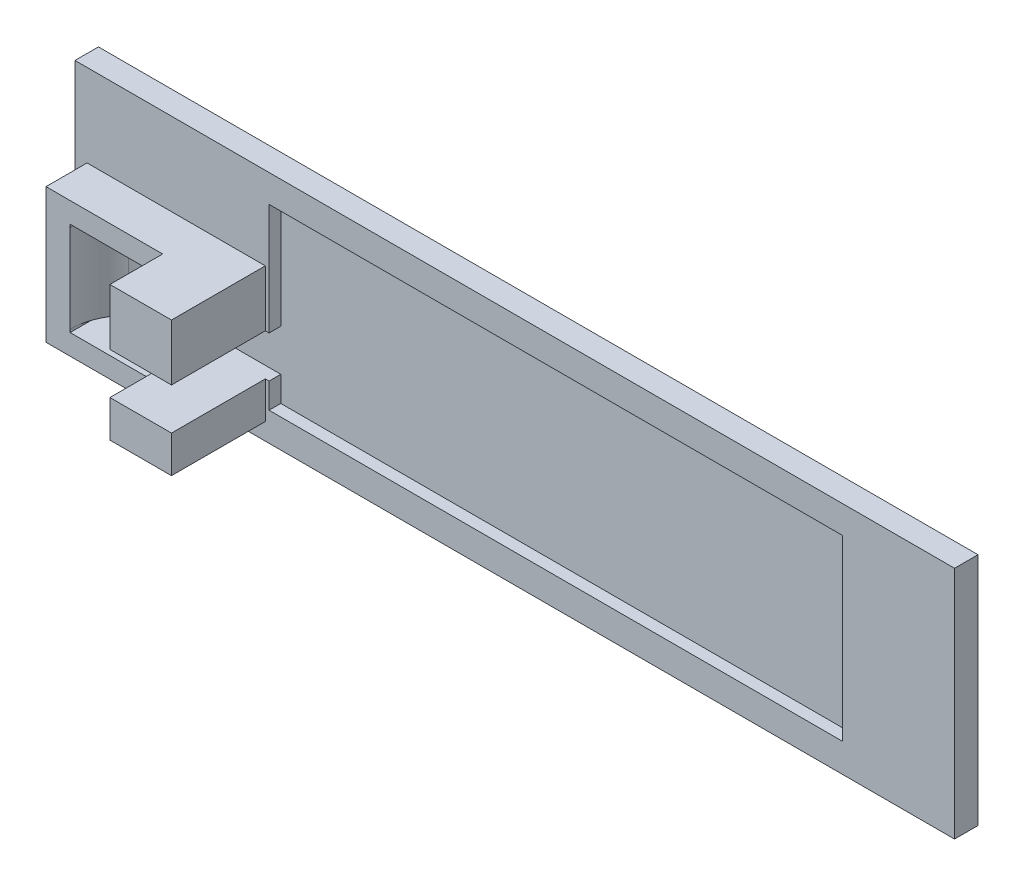
SolidWorks part; units mm, degrees
ref_plane "Front Plane" through (0, 0, 0) normal (0, 0, 1) x (1, 0, 0)
ref_plane "Top Plane" through (0, 0, 0) normal (0, 1, 0) x (1, 0, 0)
ref_plane "Right Plane" through (0, 0, 0) normal (1, 0, 0) x (0, 0, -1)
sketch "Sketch1" plane through (0, 0, 0) normal (0, 0, 1) x (1, 0, 0)
  line L13 (0, -3.5114) -> (107.0846, -3.5114) construction
  line L14 (-21.4577, 30.8029) -> (128.5423, 30.8029)
  line L15 (-21.4577, 30.8029) -> (-21.4577, -9.1971)
  line L16 (-21.4577, -9.1971) -> (128.5423, -9.1971)
  line L17 (128.5423, 30.8029) -> (128.5423, -9.1971)
  line L18 (107.0846, 25.1173) -> (107.0846, -3.5114) construction
  line L19 (0, 25.1173) -> (0, -3.5114) construction
  line L20 (0, 10.8029) -> (107.0846, 10.8029) construction
  line L21 (107.4114, 19.3947) -> (107.4114, 16.5631) construction
  line L22 (107.0846, 25.1173) -> (0, 25.1173) construction
  line L23 (-21.4577, -9.1971) -> (128.5423, 30.8029) construction
  line L24 (-21.4577, 30.8029) -> (128.5423, -9.1971) construction
  line L140 (53.5423, 25.1173) -> (53.5423, -3.5114) construction
  line L141 (107.4114, 19.3947) -> (107.4114, 16.5631)
  line L165 (11.6394, 7.1) -> (0, 7.1)
  line L167 (0, 7.1) -> (0, 0)
  line L168 (12.1959, 0) -> (0, 0)
  line L175 (47.7841, -3.3074) -> (15.7841, -3.3091)
  line L177 (59.697, 8.6) -> (51.1997, 8.6)
  line L178 (59.5311, 0) -> (51.2601, 0)
  line L181 (83.5648, 4.4251) -> (81.1572, 3.7789)
  line L182 (83.5648, 4.4251) -> (85.862, 5.0416)
  line L183 (78.4316, 11.9447) -> (84.5441, 13.5851)
  line L270 (78.4311, 0.8377) -> (63.1711, -3.2576)
  line L271 (65.5629, 16.5075) -> (72.9629, 16.4991)
  line L287 (44.696, 16.5689) -> (18.896, 16.5731)
  line L288 (107.4114, 19.3947) -> (104.0237, 19.1062)
  arc A61 (18.896, 16.5731) -> (17.2018, 15.856) centre (18.896, 14.2135) ccw
  arc A62 (11.6394, 7.1) -> (17.2018, 15.856) centre (34.8626, -1.5082) cw
  arc A66 (12.1959, 0) -> (15.7841, -3.3091) centre (15.7841, 0.2909) ccw
  arc A68 (104.0237, 19.1062) -> (86.5055, 16.4197) centre (95.503, 16.2083) ccw
  arc A69 (72.9629, 16.4991) -> (75.1629, 14.1075) centre (72.7629, 14.1075) cw
  arc A70 (63.1629, 14.1075) -> (65.5629, 16.5075) centre (65.5629, 14.1075) cw
  arc A71 (59.697, 8.6) -> (63.1629, 14.1075) centre (69.0513, 6.5576) cw
  arc A72 (75.1629, 14.1075) -> (78.4316, 11.9447) centre (72.8809, 7.1072) cw
  arc A73 (84.5441, 13.5851) -> (86.5055, 16.4197) centre (89.2522, 12.4232) cw
  arc A74 (107.4114, 16.5631) -> (90.2782, 3.8893) centre (79.9571, 35.7597) cw
  arc A76 (81.1572, 3.7789) -> (78.4311, 0.8377) centre (77.736, 4.216) cw
  arc A77 (63.1711, -3.2576) -> (59.5311, 0) centre (63.3985, 0.6589) cw
  arc A80 (51.2601, 0) -> (47.7841, -3.3074) centre (47.6719, 0.2909) cw
  arc A82 (44.696, 16.5689) -> (46.2498, 15.856) centre (44.5557, 14.2135) cw
  arc A91 (51.1997, 8.6) -> (46.2498, 15.856) centre (28.5891, -1.5082) ccw
  arc A94 (85.862, 5.0416) -> (90.2782, 3.8893) centre (89.803, 11.1066) ccw
  dimension "D9" = 9
  dimension "D10" = 33.5
  dimension "D1" = 40
  dimension "D2" = 150
  dimension "D3" = 7.1
  dimension "D4" = 32
  dimension "D5" = 25.8
  dimension "D6" = 15.8
  dimension "D7" = 7.4
  dimension "D8" = 3.4
extrude "Boss-Extrude1" add sketch "Sketch1" along normal blind 2
sketch "Sketch2" plane through (0, 0, 0) normal (0, 0, 1) x (1, 0, 0)
  line L1 (-21.4577, 30.8029) -> (128.5423, 30.8029)
  line L2 (-21.4577, 30.8029) -> (-21.4577, -9.1971)
  line L3 (-21.4577, -9.1971) -> (128.5423, -9.1971)
  line L4 (128.5423, 30.8029) -> (128.5423, -9.1971)
extrude "Boss-Extrude2" add sketch "Sketch2" against normal blind 2
sketch "Sketch3" plane through (0, 0, 0) normal (0, 1, 0) x (1, 0, 0)
  line L0 (0, -2) -> (-5.5, -2) construction
  line L1 (128.5423, -2) -> (-21.4577, -2) construction
  line L2 (-5.5, -2) -> (-5.5, -9.2) construction
  line L3 (-5.5, -9.2) -> (0, -9.2) construction
  line L4 (0, -9.2) -> (0, -0.8) construction
  line L5 (0, -0.8) -> (0, -17.6)
  arc A1 (0, -0.8) -> (0, -17.6) centre (-5.5, -9.2) ccw
  dimension "D3" = 8.4
  dimension "D1" = 5.5
  dimension "D2" = 7.2
extrude "Cut-Extrude1" cut sketch "Sketch3" along normal blind 12.7 and the other way blind 2.3
sketch "Sketch4" plane through (0, 0, 0) normal (0, 0, 1) x (1, 0, 0)
  line L0 (0, 7.1) -> (0, 12.7)
  line L1 (0, 12.7) -> (-12.4979, 12.7)
  line L3 (-12.3455, 16.6971) -> (4, 16.6971)
  line L6 (11, 7.1) -> (0, 7.1)
  line L7 (0, 0) -> (0, -2.3)
  line L8 (0, -2.3) -> (-12.4979, -2.3)
  line L10 (-12.3454, -6.2971) -> (4, -6.2971)
  line L12 (0, 0) -> (12.1959, 0) construction
  line L13 (11, 0) -> (0, 0)
  line L14 (-12.3454, -6.2971) -> (-15.3454, -6.2971)
  line L15 (-15.3454, -6.2971) -> (-15.3454, -2.3)
  line L16 (-15.3454, -2.3) -> (-12.4979, -2.3)
  line L17 (-12.3455, 16.6971) -> (-15.3454, 16.6971)
  line L18 (-15.3454, 16.6971) -> (-15.3454, 12.7)
  line L19 (-15.3454, 12.7) -> (-12.4979, 12.7)
  line L20 (4, 16.6971) -> (11, 16.6971)
  line L21 (11, 16.6971) -> (11, 7.1)
  line L22 (11.6394, 7.1) -> (0, 7.1) construction
  line L23 (4, -6.2971) -> (11, -6.2971)
  line L24 (11, -6.2971) -> (11, 0)
  dimension "D1" = 4
  dimension "D3" = 4
  dimension "D5" = 16.3454
  dimension "D6" = 3
  dimension "D7" = 7
extrude "Boss-Extrude3" add sketch "Sketch4" along normal blind 9
sketch "Sketch5" plane through (0, 0, 0) normal (0, 1, 0) x (1, 0, 0)
  line L1 (-5.5, -2) -> (-5.5, -9) construction
  line L2 (-5.5546, -9) -> (0, -9) construction
  line L3 (0, -9) -> (0, -0.9) construction
  line L5 (0, 0) -> (0, -0.9) construction
  line L6 (-15.2908, -9) -> (-19.4001, -9)
  line L7 (-19.4001, -9) -> (-19.4001, -2)
  line L8 (128.5423, -2) -> (-21.4577, -2) construction
  line L9 (-19.4001, -2) -> (-12.3454, -2)
  line L11 (-5.5, -9) -> (0, -9) construction
  line L12 (0, -9) -> (0, -0.9) construction
  arc A1 (-12.3454, -2) -> (-15.2908, -9) centre (-5.5, -9) ccw
  dimension "D2" = 7
  dimension "D3" = 8.1
  dimension "D4" = 0.9
  dimension "D5" = 8.1
extrude "Boss-Extrude4" add sketch "Sketch5" along normal up to surface and the other way up to surface up to face at (-2.1727, 16.6971, 5.5) other way up to face at (-2.1727, -6.2971, 5.5)
sketch "Sketch6" plane through (0, 0, 9) normal (0, 0, 1) x (1, 0, 0)
  line L0 (0, 7.1) -> (0, 12.7)
  line L1 (0, 12.7) -> (-15.2908, 12.7)
  line L4 (-15.2908, -2.3) -> (0, -2.3)
  line L5 (0, -2.3) -> (0, 0)
  line L6 (0, 0) -> (0.5, 0)
  line L7 (11, 0) -> (0, 0) construction
  line L8 (0.5, 0) -> (0.5, -2.8)
  line L9 (0.5, -2.8) -> (-15.2908, -2.8)
  line L11 (-15.2908, 13.2) -> (0.5, 13.2)
  line L12 (0.5, 13.2) -> (0.5, 7.1)
  line L13 (0, 7.1) -> (11, 7.1) construction
  line L14 (0.5, 7.1) -> (0, 7.1)
  line L15 (-15.2908, 12.7) -> (-15.2908, 13.2)
  line L16 (-15.2908, -2.3) -> (-15.2908, -2.8)
  line L17 (-15.2908, 12.7) -> (-15.2908, -2.3) construction
  dimension "D1" = 0.5
  dimension "D2" = 0.5
  dimension "D4" = 0.5
extrude "Cut-Extrude2" cut sketch "Sketch6" against normal up to surface (9 mm away) up to face at (57.9016, 9.0957, 0)
sketch "Sketch7" plane through (0, 0, 2) normal (0, 0, 1) x (1, 0, 0)
  line L0 (11.6394, 7.1) -> (11.6394, 26.1)
  line L1 (11.6394, 26.1) -> (109.4114, 26.1)
  line L2 (109.4114, 26.1) -> (109.4114, -4.3082)
  line L4 (11.6394, -4.3082) -> (109.4114, -4.3082)
  line L5 (11.6394, 7.1) -> (11.6394, -4.3082)
  dimension "D1" = 19
  dimension "D2" = 97.772
extrude "Cut-Extrude3" cut sketch "Sketch7" against normal blind 2
sketch "Sketch8" plane through (0, 0, 9) normal (0, 0, 1) x (1, 0, 0)
  line L0 (-19.4001, -6.2971) -> (11, -6.2971) construction
  line L1 (0.5, 7.1) -> (11, 7.1)
  line L2 (0.5, 7.1) -> (0.5, 16.6971)
  line L3 (0.5, 16.6971) -> (11, 16.6971)
  line L4 (11, 7.1) -> (11, 16.6971)
  line L5 (11, 0) -> (0.5, 0)
  line L6 (11, 0) -> (11, -6.2971)
  line L7 (11, -6.2971) -> (0.5, -6.2971)
  line L8 (0.5, 0) -> (0.5, -6.2971)
extrude "Boss-Extrude5" add sketch "Sketch8" along normal blind 9
